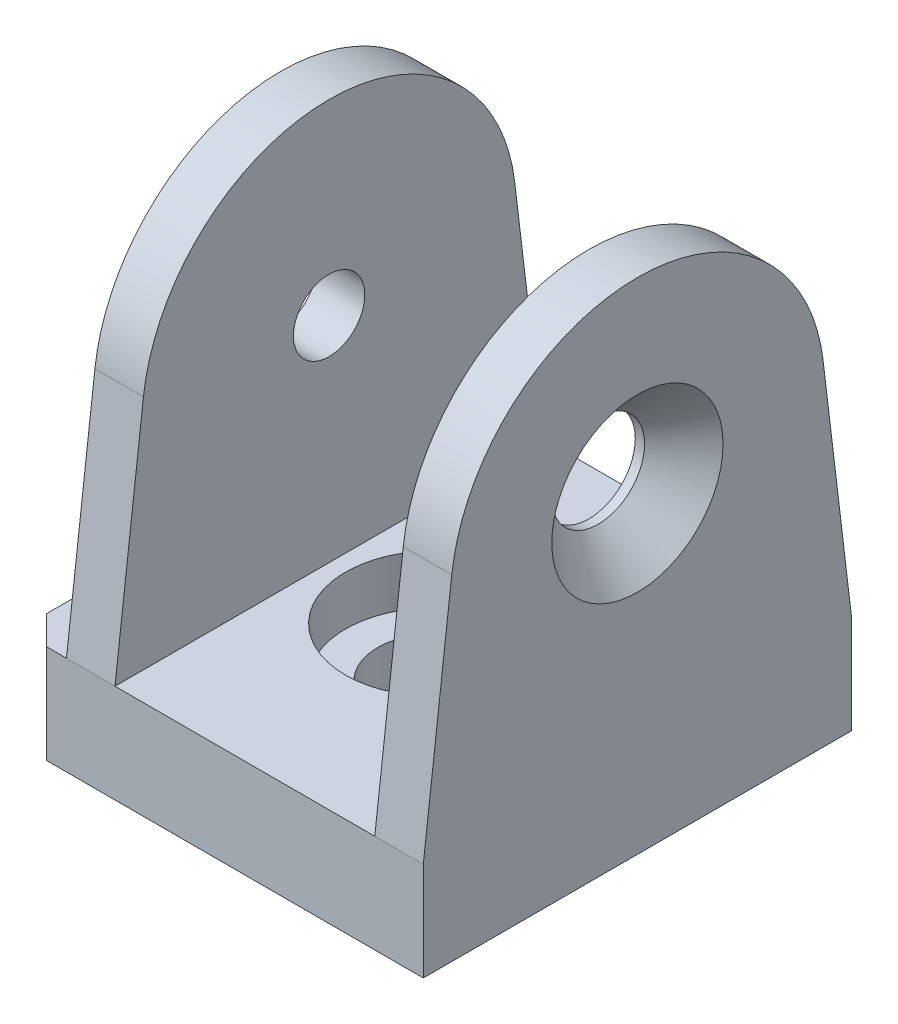
SolidWorks part; units mm, degrees
material "Алюминиевый сплав"
ref_plane "Спереди" through (0, 0, 0) normal (0, 0, 1) x (1, 0, 0)
ref_plane "Сверху" through (0, 0, 0) normal (0, 1, 0) x (1, 0, 0)
ref_plane "Справа" through (0, 0, 0) normal (1, 0, 0) x (0, 0, -1)
sketch "Эскиз1" plane through (0, 0, 0) normal (0, 1, 0) x (1, 0, 0)
  line L1 (14.2, -15) -> (-14.2, -15)
  line L2 (14.2, -15) -> (14.2, 15)
  line L3 (14.2, 15) -> (-14.2, 15)
  line L4 (-14.2, -15) -> (-14.2, 15)
  line L5 (14.2, -15) -> (-14.2, 15) construction
  line L6 (14.2, 15) -> (-14.2, -15) construction
  point P0 (0, 0)
  dimension "D1" = 28.4
  dimension "D2" = 30
extrude "Бобышка-Вытянуть1" add sketch "Эскиз1" along normal blind 6.9
sketch "Эскиз2" plane through (0, 0, 0) normal (0, 0, 1) x (1, 0, 0)
  line L1 (-14.2, 0) -> (14.2, 0) construction
  line L2 (-4, 0) -> (-4, 3.45)
  line L3 (-4, 3.45) -> (-6.25, 3.45)
  line L4 (-6.25, 3.45) -> (-6.25, 6.9)
  line L5 (-14.2, 6.9) -> (14.2, 6.9) construction
  line L7 (0, 6.9) -> (0, 0) construction
  line L11 (-14.2, 6.9) -> (-14.2, 0) construction
  line L12 (-6.25, 6.9) -> (0, 6.9)
  line L13 (0, 0) -> (-4, 0)
  line L14 (0, 0) -> (0, 6.9)
  point P17 (-14.2, 3.45)
  dimension "D1" = 8
  dimension "D2" = 12.5
revolve "Вырез-Повернуть1" cut sketch "Эскиз2" angle 360 about L7
sketch "Эскиз3" plane through (14.2, 0, 0) normal (1, 0, 0) x (0, 0, -1)
  line L0 (-15, 6.9) -> (-13.0061, 23.4655)
  line L1 (13.0061, 23.4655) -> (15, 6.9)
  line L2 (15, 6.9) -> (-15, 6.9)
  line L3 (-15, 0) -> (15, 0) construction
  arc A0 (-13.0061, 23.4655) -> (13.0061, 23.4655) centre (0, 21.9) cw
  dimension "D1" = 35
  dimension "D2" = 15
extrude "Бобышка-Вытянуть2" add sketch "Эскиз3" against normal blind 25
sketch "Эскиз4" plane through (0, 0, 0) normal (0, 0, 1) x (1, 0, 0)
  line L0 (-10.8, 6.9) -> (14.2, 6.9) construction
  line L1 (10.8, 6.9) -> (-7.4, 6.9)
  line L2 (10.8, 6.9) -> (10.8, 35)
  line L3 (10.8, 35) -> (-7.4, 35)
  line L4 (-7.4, 6.9) -> (-7.4, 35)
  line L5 (14.2, 35) -> (-10.8, 35) construction
  line L6 (10.8, 20.95) -> (14.2, 20.95) construction
  line L7 (14.2, 23.4655) -> (14.2, 6.9) construction
  line L8 (-7.4, 20.95) -> (-10.8, 20.95) construction
  line L9 (-10.8, 23.4655) -> (-10.8, 6.9) construction
  dimension "D1" = 3.4
extrude "Вырез-Вытянуть1" cut sketch "Эскиз4" against normal through all and the other way through all
chamfer "Фаска1" distance 2 angle 45 2 edges at (-14.2, 3.45, -15) (-14.2, 3.45, 15)
hole_wizard "Отверстие обработанное метчиком M61" positions "Эскиз5" profile "Эскиз7" tap size "M6" standard "ISO" end condition up to next
sketch "Эскиз5" plane through (-10.8, 0, 0) normal (-1, 0, 0) x (0, 0, 1)
  point P0 (0, 21.9)
sketch "Эскиз7" plane through (-10.8, 21.9, 0) normal (0, 1, 0) x (0, 0, 1)
  line L0 (0, 0) -> (0, 3.4)
  line L1 (0, 3.4) -> (2.5, 3.4)
  line L2 (2.5, 3.4) -> (2.5, 0)
  line L5 (2.5, 0) -> (0, 0)
  line L11 (0, -6.35) -> (0, 107.95) construction
  dimension "Диаметр проходного сверла" = 5
  dimension "Глубина проходного сверла" = 3.4
cosmetic thread "Отверстие резьбы1" parameters "D2"=6
hole_wizard "Зенковка для винта с полупотайной головкой 1" positions "Эскиз8" profile "Эскиз10" countersink size "M6" standard "ISO" end condition up to next
sketch "Эскиз8" plane through (14.2, 0, 0) normal (1, 0, 0) x (0, 0, -1)
  point P0 (0, 21.9)
sketch "Эскиз10" plane through (14.2, 21.9, 0) normal (0, 1, 0) x (0, 0, -1)
  line L0 (0, 0) -> (0, 3.4)
  line L1 (0, 3.4) -> (3.25, 3.4)
  line L2 (3.25, 3.4) -> (3.25, 2.75)
  line L3 (3.25, 2.75) -> (6, 0)
  line L5 (6, 0) -> (0, 0)
  line L6 (-3.25, 2.75) -> (-6, 0) construction
  line L11 (0, -6.35) -> (0, 107.95) construction
  dimension "Диаметр сквозного отверстия" = 6.5
  dimension "Глубина сквозного отверстия" = 3.4
  dimension "Диаметр передней зенковки" = 12
  dimension "Угол передней зенковки" = 90
